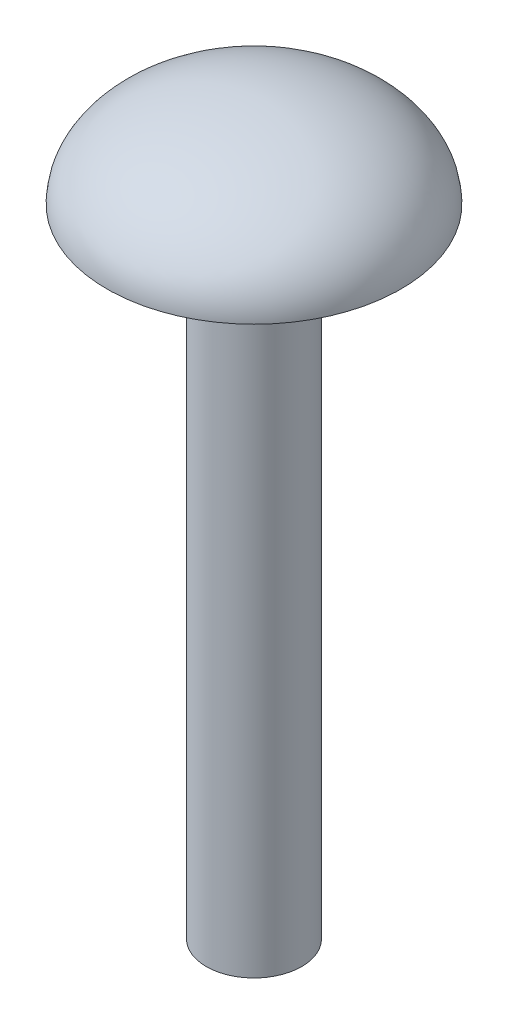
SolidWorks part; units mm, degrees
ref_plane "Front Plane" through (0, 0, 0) normal (0, 0, 1) x (1, 0, 0)
ref_plane "Top Plane" through (0, 0, 0) normal (0, 1, 0) x (1, 0, 0)
ref_plane "Right Plane" through (0, 0, 0) normal (1, 0, 0) x (0, 0, -1)
sketch "Sketch2" plane through (0, 0, 0) normal (0, 0, 1) x (1, 0, 0)
  line L0 (-4.62, 0) -> (0, 0)
  line L1 (0, 0) -> (0, 2.81)
  ellipse E0 centre (0, 0) end of major axis (-4.62, 0) minor radius 2.81 (0, 2.81) -> (-4.62, 0) ccw
  dimension "D1" = 9.24
  dimension "D2" = 5.62
revolve "Revolve1" add sketch "Sketch2" angle 360 about L1
sketch "Sketch3" plane through (0, 0, 0) normal (0, 1, 0) x (1, 0, 0)
  circle A0 centre (0, 0) radius 1.4997
extrude "Boss-Extrude1" add sketch "Sketch3" against normal blind 20
